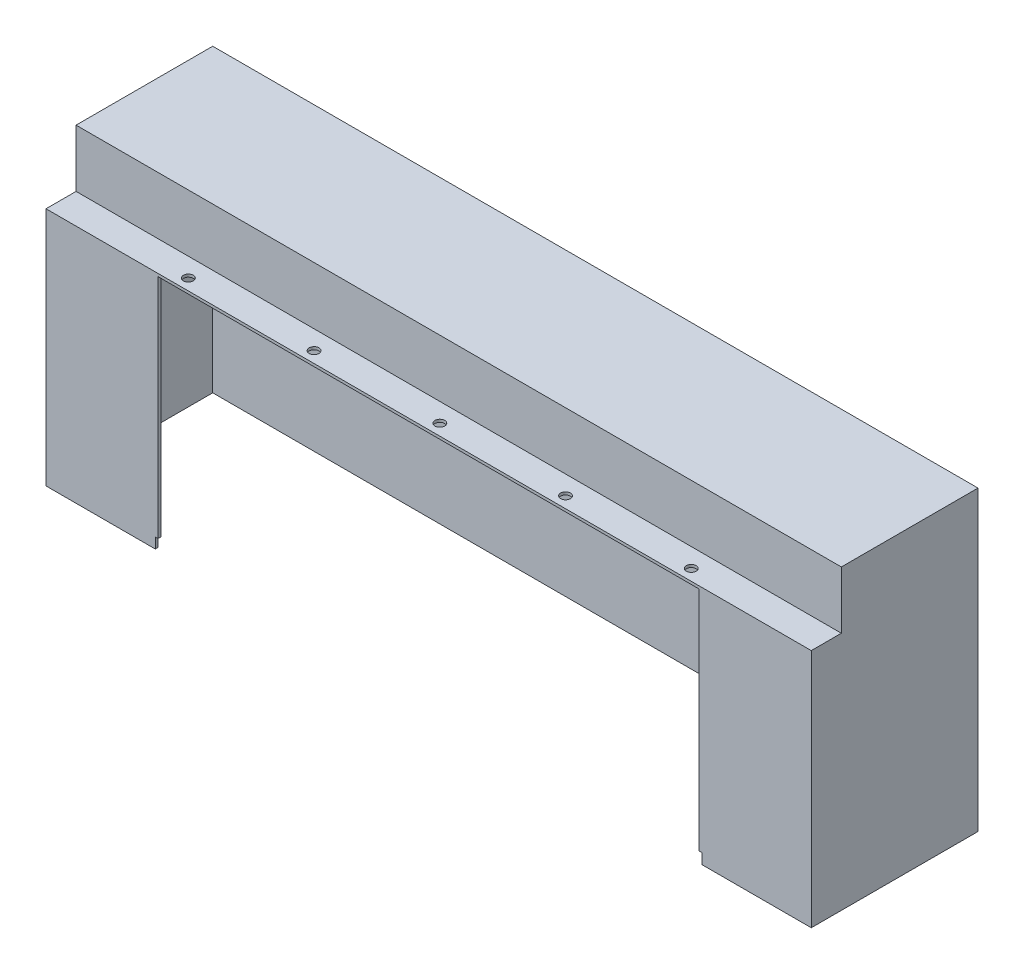
SolidWorks part; units mm, degrees
ref_plane "Plano frontal" through (0, 0, 0) normal (0, 0, 1) x (1, 0, 0)
ref_plane "Plano superior" through (0, 0, 0) normal (0, 1, 0) x (1, 0, 0)
ref_plane "Plano direito" through (0, 0, 0) normal (1, 0, 0) x (0, 0, -1)
sketch "Esboço1" plane through (0, 0, 0) normal (0, 0, 1) x (1, 0, 0)
  line L1 (350, -105) -> (-350, -105)
  line L2 (350, -105) -> (350, 105)
  line L3 (350, 105) -> (-350, 105)
  line L4 (-350, -105) -> (-350, 105)
  line L5 (350, -105) -> (-350, 105) construction
  line L6 (350, 105) -> (-350, -105) construction
  point P0 (0, 0)
  dimension "D1" = 700
  dimension "D2" = 210
extrude "Ressalto-extrusão1" add sketch "Esboço1" along normal blind 2.5
sketch "Esboço2" plane through (0, 0, 2.5) normal (0, 0, 1) x (1, 0, 0)
  line L0 (-347.5, 102.5) -> (-347.5, -105)
  line L1 (-350, -105) -> (350, -105) construction
  line L2 (350, -105) -> (347.5, -105)
  line L3 (347.5, 102.5) -> (-347.5, 102.5)
  line L4 (-350, 105) -> (-350, -105)
  line L5 (-350, -105) -> (350, -105)
  line L6 (350, -105) -> (350, 105)
  line L7 (350, 105) -> (-350, 105)
  line L8 (-350, 105) -> (-350, -105)
  line L9 (347.5, 102.5) -> (347.5, -105)
  line L10 (350, -105) -> (350, 105)
  line L11 (350, 105) -> (-350, 105)
  line L12 (-347.5, -105) -> (-350, -105)
  line L16 (-347.5, -102.5) -> (347.5, -102.5) construction
  line L17 (-350, -105) -> (350, -105) construction
  line L18 (-347.5, 102.5) -> (-347.5, -102.5) construction
  line L19 (347.5, -102.5) -> (347.5, 102.5) construction
  dimension "D1" = 0
  dimension "D2" = 2.5
extrude "Ressalto-extrusão2" add sketch "Esboço2" along normal blind 150
sketch "Esboço3" plane through (0, 105, 0) normal (0, 1, 0) x (1, 0, 0)
  line L0 (350, 0) -> (-350, 0) construction
  line L5 (-350, -152.5) -> (-350, 0) construction
  line L6 (-347.5, -122.5) -> (347.5, -122.5)
  line L7 (-347.5, -122.5) -> (-347.5, -2.5)
  line L8 (-347.5, -2.5) -> (347.5, -2.5)
  line L9 (347.5, -122.5) -> (347.5, -2.5)
  line L12 (350, -152.5) -> (350, 0) construction
  dimension "D1" = 2.5
  dimension "D3" = 120
  dimension "D4" = 2.5
  dimension "D5" = 2.5
extrude "Corte-extrusão3" cut sketch "Esboço3" against normal up to next contours L9 L8 L7 L6
sketch "Esboço6" plane through (0, -105, 0) normal (0, -1, 0) x (1, 0, 0)
  line L4 (0, 0) -> (0, -59.9119) construction
  line L5 (350, 152.5) -> (347.5, 152.5)
  line L6 (-350, 0) -> (350, 0)
  line L7 (-350, 0) -> (350, 0)
  line L8 (350, 0) -> (350, 152.5)
  line L9 (350, 0) -> (350, 152.5)
  line L16 (350, 152.5) -> (347.5, 152.5)
  line L17 (347.5, 152.5) -> (347.5, 2.5)
  line L20 (347.5, 2.5) -> (-347.5, 2.5)
  line L21 (347.5, 2.5) -> (-347.5, 2.5)
  line L22 (-347.5, 2.5) -> (-347.5, 152.5)
  line L23 (-347.5, 2.5) -> (-347.5, 152.5)
  line L24 (-347.5, 152.5) -> (-350, 152.5)
  line L25 (347.5, 152.5) -> (347.5, 2.5)
  line L26 (-347.5, 152.5) -> (-350, 152.5)
  line L27 (-350, 152.5) -> (-350, 0)
  line L28 (-350, 152.5) -> (-350, 0)
  dimension "D1" = 0
extrude "Ressalto-extrusão5" add sketch "Esboço6" along normal blind 9.58
sketch "Esboço7" plane through (347.5, 0, 0) normal (-1, 0, 0) x (0, 0, 1)
  line L0 (152.5, 102.5) -> (122.5, 102.5) construction
  line L2 (152.5, -114.58) -> (150, -114.58)
  line L4 (152.5, -114.58) -> (152.5, 102.5)
  line L6 (152.5, 102.5) -> (150, 102.5)
  line L7 (150, -114.58) -> (150, 102.5)
  dimension "D1" = 2.5
extrude "Ressalto-extrusão6" add sketch "Esboço7" along normal blind 100
mirror "Espelhar1" about plane through (0, 0, 0) normal (1, 0, 0) of "Ressalto-extrusão6"
sketch "Esboço9" plane through (0, 0, 152.5) normal (0, 0, 1) x (1, 0, 0)
  line L0 (0, 0) -> (0, -34.1825) construction
  line L1 (-247.5, -114.58) -> (-250, -114.58)
  line L2 (-247.5, -114.58) -> (-247.5, -104.98)
  line L3 (-247.5, -104.98) -> (-250, -104.98)
  line L4 (-250, -114.58) -> (-250, -104.98)
  line L5 (250, -114.58) -> (250, -104.98)
  line L6 (247.5, -104.98) -> (250, -104.98)
  line L7 (247.5, -114.58) -> (247.5, -104.98)
  line L8 (247.5, -114.58) -> (250, -114.58)
  dimension "D1" = 2.5
  dimension "D2" = 9.6
extrude "Corte-extrusão4" cut sketch "Esboço9" against normal blind 9.5
sketch "Esboço10" plane through (0, 105, 0) normal (0, 1, 0) x (1, 0, 0)
  circle A0 centre (-230, -142.29) radius 4.5
  circle A1 centre (-115, -142.29) radius 4.5
  circle A2 centre (0, -142.29) radius 4.5
  circle A3 centre (115, -142.29) radius 4.5
  circle A4 centre (230, -142.29) radius 4.5
  dimension "D1" = 9
extrude "Corte-extrusão5" cut sketch "Esboço10" against normal blind 3
sketch "Esboço11" plane through (0, 105, 0) normal (0, 1, 0) x (1, 0, 0)
  line L0 (-350, -125) -> (350, -125)
  line L1 (350, -152.5) -> (350, 0) construction
  line L2 (-347.5, -122.5) -> (347.5, -122.5) construction
  line L3 (-347.5, -122.5) -> (-347.5, -2.5) construction
  line L4 (350, 0) -> (-350, 0)
  line L5 (-350, 0) -> (-350, -152.5)
  line L6 (-350, -152.5) -> (350, -152.5)
  line L7 (350, -152.5) -> (350, 0)
  line L8 (350, 0) -> (-350, 0)
  line L9 (-350, 0) -> (-350, -125)
  line L10 (-347.5, -2.5) -> (347.5, -2.5) construction
  line L11 (350, -125) -> (350, 0)
  line L12 (347.5, -122.5) -> (347.5, -2.5) construction
  line L13 (-347.5, -122.5) -> (-347.5, -2.5)
  line L14 (-347.5, -122.5) -> (347.5, -122.5)
  line L15 (-347.5, -2.5) -> (347.5, -2.5)
  line L16 (347.5, -122.5) -> (347.5, -2.5)
  dimension "D2" = 2.5
  dimension "D1" = 0
extrude "Ressalto-extrusão7" add sketch "Esboço11" along normal blind 50
sketch "Esboço12" plane through (0, 155, 0) normal (0, 1, 0) x (1, 0, 0)
  line L4 (350, -125) -> (350, 0)
  line L5 (350, 0) -> (-350, 0)
  line L6 (-350, 0) -> (-350, -125)
  line L7 (-350, -125) -> (350, -125)
  line L8 (350, -125) -> (350, 0)
  line L9 (350, 0) -> (-350, 0)
  line L10 (-350, 0) -> (-350, -125)
  line L11 (-350, -125) -> (350, -125)
  dimension "D1" = 0
extrude "Ressalto-extrusão8" add sketch "Esboço12" along normal blind 2.5
